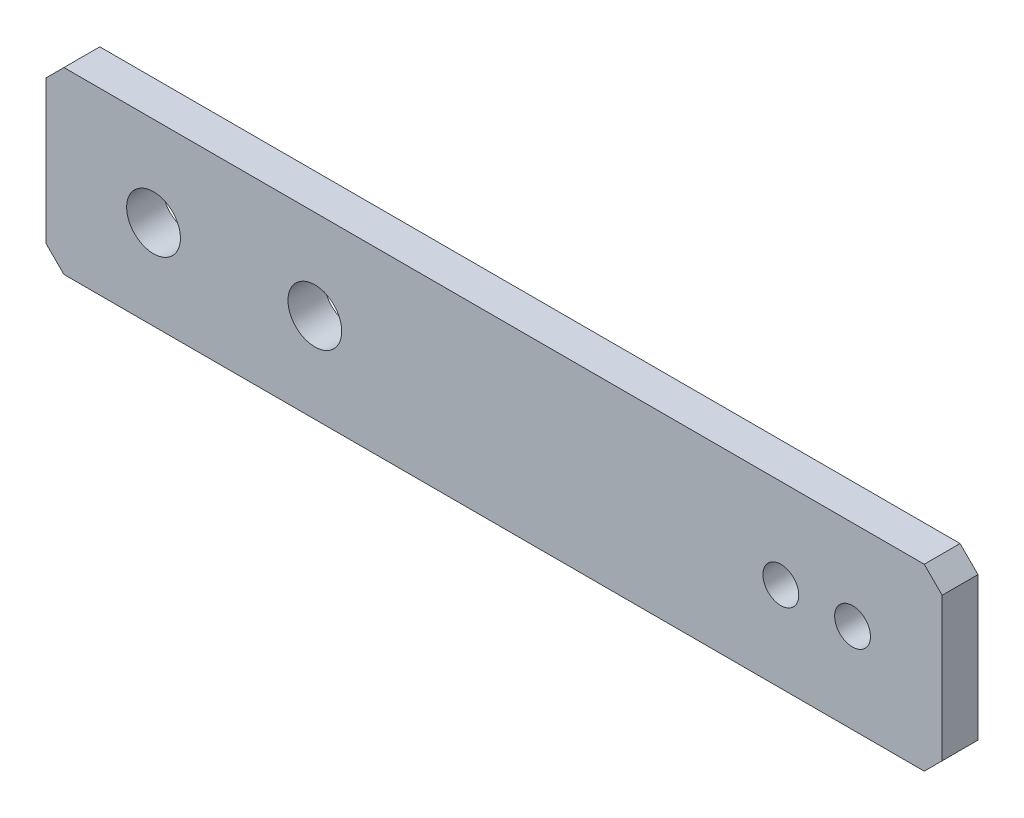
SolidWorks part; units mm, degrees
ref_plane "Front Plane" through (0, 0, 0) normal (0, 0, 1) x (1, 0, 0)
ref_plane "Top Plane" through (0, 0, 0) normal (0, 1, 0) x (1, 0, 0)
ref_plane "Right Plane" through (0, 0, 0) normal (1, 0, 0) x (0, 0, -1)
sketch "Sketch1" plane through (0, 0, 0) normal (0, 0, 1) x (1, 0, 0)
  line L1 (-14.1707, 9.38) -> (35.8293, 9.38)
  line L2 (-14.1707, 9.38) -> (-14.1707, -0.62)
  line L3 (-14.1707, -0.62) -> (35.8293, -0.62)
  line L4 (35.8293, 9.38) -> (35.8293, -0.62)
  circle A0 centre (-8.1707, 4.38) radius 1.5
  circle A1 centre (0.8293, 4.38) radius 1.5
  circle A2 centre (26.8293, 4.38) radius 1
  circle A3 centre (30.8293, 4.38) radius 1
  dimension "D3" = 3
  dimension "D4" = 2
  dimension "D5" = 9
  dimension "D6" = 4
  dimension "D7" = 5
  dimension "D1" = 50
  dimension "D2" = 10
  dimension "D8" = 6
extrude "Boss-Extrude1" add sketch "Sketch1" along normal blind 2
chamfer "Chamfer1" distance 1 angle 45 4 edges at (35.8293, 9.38, 1) (35.8293, -0.62, 1) (-14.1707, -0.62, 1) (-14.1707, 9.38, 1)
